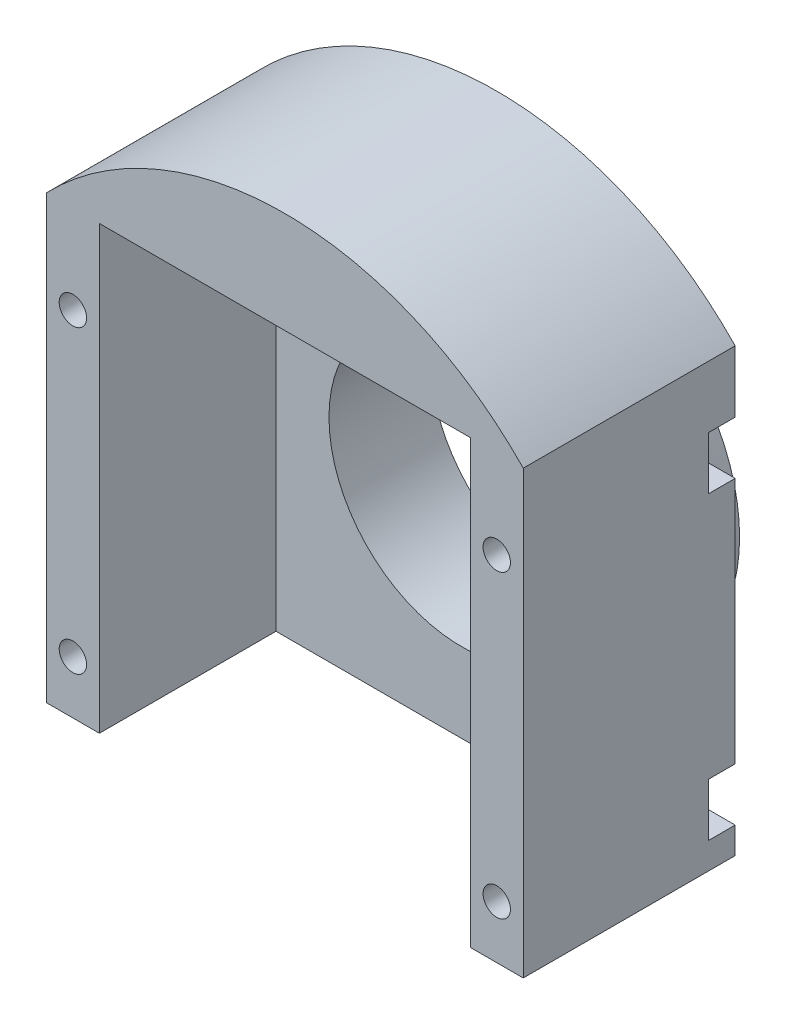
SolidWorks part; units mm, degrees
ref_plane "前视基准面" through (0, 0, 0) normal (0, 0, 1) x (1, 0, 0)
ref_plane "上视基准面" through (0, 0, 0) normal (0, 1, 0) x (1, 0, 0)
ref_plane "右视基准面" through (0, 0, 0) normal (1, 0, 0) x (0, 0, -1)
sketch "草图1" plane through (0, 0, 0) normal (0, 0, 1) x (1, 0, 0)
  line L1 (-27, 25) -> (27, 25)
  line L2 (-27, 25) -> (-27, -25)
  line L3 (-27, -25) -> (27, -25)
  line L4 (27, 25) -> (27, -25)
  line L5 (0, -25) -> (0, 25) construction
  line L6 (-27, 0) -> (27, 0) construction
  point P0 (0, 0)
  dimension "D1" = 50
  dimension "D2" = 54
extrude "凸台-拉伸1" add sketch "草图1" along normal blind 24
sketch "草图2" plane through (0, 0, 24) normal (0, 0, 1) x (1, 0, 0)
  line L0 (-27, 25) -> (-27, -25) construction
  line L1 (27, 25) -> (-27, 25) construction
  line L3 (-24, 15) -> (24, 15) construction
  line L4 (-27, -25) -> (27, -25) construction
  circle A0 centre (-24, 15) radius 1.55
  circle A1 centre (24, 15) radius 1.55
  circle A2 centre (24, -19) radius 1.55
  circle A3 centre (-24, -19) radius 1.55
  dimension "D1" = 3.1
  dimension "D6" = 48
  dimension "D2" = 3
  dimension "D3" = 10
  dimension "D7" = 6
  dimension "D4" = 2
  dimension "D5" = 2
extrude "切除-拉伸1" cut sketch "草图2" against normal through all
sketch "草图3" plane through (0, 0, 24) normal (0, 0, 1) x (1, 0, 0)
  line L0 (27, 25) -> (-27, 25) construction
  line L1 (-27, 25) -> (27, 25)
  arc A0 (-27, 25) -> (27, 25) centre (0, -1) cw
  dimension "D1" = 26
extrude "凸台-拉伸2" add sketch "草图3" against normal up to surface (24 mm away) up to face at (-22.45, -19, 0)
sketch "草图5" plane through (0, 0, 24) normal (0, 0, 1) x (1, 0, 0)
  line L0 (21, 25) -> (21, -25)
  line L1 (-27, -25) -> (27, -25) construction
  line L2 (21, -25) -> (-21, -25)
  line L3 (-21, -25) -> (-21, 25)
  line L4 (0, 25) -> (0, -34.0506) construction
  line L5 (-21, 25) -> (21, 25)
  dimension "D1" = 50
  dimension "D2" = 42
extrude "切除-拉伸3" cut sketch "草图5" against normal blind 20
sketch "草图6" plane through (0, 0, 0) normal (0, 0, -1) x (-1, 0, 0)
  line L0 (-27, -16) -> (-24, -16)
  line L1 (-27, -25) -> (-27, 25) construction
  line L2 (-24, -22) -> (-27, -22)
  line L3 (-27, -16) -> (-27, -22)
  line L4 (-27, 18) -> (-27, 12)
  line L5 (-24, 12) -> (-27, 12)
  line L6 (-27, 18) -> (-24, 18)
  line L7 (-27, -16) -> (-27, 18) construction
  line L8 (0, 40.7864) -> (0, -44.4319) construction
  line L9 (27, -16) -> (24, -16)
  line L10 (24, -22) -> (27, -22)
  line L11 (27, -16) -> (27, -22)
  line L12 (27, 18) -> (24, 18)
  line L13 (24, 12) -> (27, 12)
  line L14 (27, 18) -> (27, 12)
  arc A0 (-24, -16) -> (-24, -22) centre (-24, -19) cw
  circle A1 centre (-24, -19) radius 1.55 construction
  arc A2 (-24, 18) -> (-24, 12) centre (-24, 15) cw
  arc A3 (24, -16) -> (24, -22) centre (24, -19) ccw
  arc A4 (24, 18) -> (24, 12) centre (24, 15) ccw
  dimension "D1" = 3
  dimension "D3" = 34
  dimension "D2" = 2
extrude "切除-拉伸4" cut sketch "草图6" against normal blind 3
sketch "草图7" plane through (0, 0, 0) normal (0, 0, -1) x (-1, 0, 0)
  line L0 (-27, 25) -> (27, 25) construction
  circle A0 centre (0, -1) radius 15
  point P0 (0, -1)
  dimension "D2" = 30
  dimension "D1" = 26
extrude "切除-拉伸5" cut sketch "草图7" against normal through all
sketch "草图8" plane through (0, 0, 0) normal (0, 0, -1) x (-1, 0, 0)
  circle A0 centre (0, -1) radius 18.55
  dimension "D1" = 37.1
sketch "草图9" plane through (0, 0, 0) normal (0, 0, -1) x (-1, 0, 0)
  line L0 (-27, -16) -> (-27, 12) construction
  line L1 (-27, 0) -> (27, 0)
  line L2 (-27, 0) -> (-27, -25)
  line L3 (-27, -25) -> (27, -25)
  line L4 (27, 0) -> (27, -25)
extrude "切除-拉伸7" [suppressed] cut sketch "草图9" against normal blind 10
fillet "圆角1" [suppressed] radius 5
sketch "草图10" [suppressed] plane through (0, 0, 0) normal (0, 0, -1) x (-1, 0, 0)
  line L0 (0, 13.8195) -> (0, -28.1113) construction
  line L1 (-18.523, 0) -> (-27, 0) construction
  circle A0 centre (-22.7615, 0) radius 2.5
  circle A1 centre (22.7615, 0) radius 2.5
  dimension "D1" = 5
extrude "切除-拉伸8" [suppressed] cut sketch "草图10" against normal up to surface (6 mm away)
sketch "草图11" plane through (0, 0, 0) normal (0, 0, -1) x (-1, 0, 0)
  circle A0 centre (0, -1) radius 20
  circle A1 centre (0, -1) radius 15
  dimension "D1" = 40
  dimension "D2" = 30
extrude "凸台-拉伸3" add sketch "草图11" along normal blind 7.5
sketch "草图12" plane through (0, 0, 0) normal (0, 0, -1) x (-1, 0, 0)
  circle A0 centre (0, -1) radius 21
  circle A1 centre (0, -1) radius 20
  dimension "D1" = 42
  dimension "D2" = 40
extrude "凸台-拉伸4" add sketch "草图12" along normal blind 0.5
